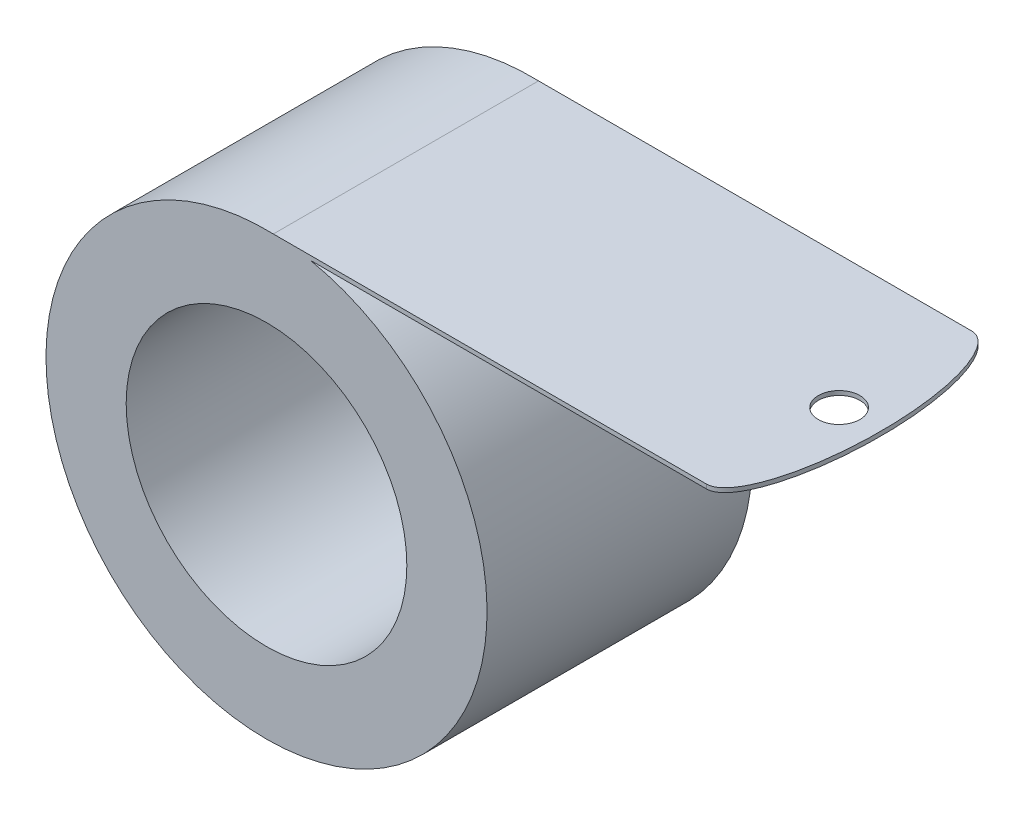
SolidWorks part; units mm, degrees
ref_plane "Front Plane" through (0, 0, 0) normal (0, 0, 1) x (1, 0, 0)
ref_plane "Top Plane" through (0, 0, 0) normal (0, 1, 0) x (1, 0, 0)
ref_plane "Right Plane" through (0, 0, 0) normal (1, 0, 0) x (0, 0, -1)
sketch "Sketch1" plane through (0, 0, 0) normal (0, 0, 1) x (1, 0, 0)
  circle A0 centre (0, 0) radius 26.4033
  circle A1 centre (0, 0) radius 16.8021
  dimension "D1" = 52.8066
  dimension "D2" = 33.6042
extrude "Boss-Extrude1" add sketch "Sketch1" along normal blind 31.75
ref_plane "Plane1" through (0, 25.8826, 0) normal (0, 1, 0) x (1, 0, 0)
sketch "Sketch2" plane through (0, 25.8826, 0) normal (0, 1, 0) x (1, 0, 0)
  line L0 (-26.4033, -31.75) -> (26.4033, -31.75) construction
  line L1 (-26.4033, -31.75) -> (26.4033, -31.75) construction
  line L2 (26.4033, 0) -> (-26.4033, 0) construction
  line L3 (26.4033, 0) -> (-26.4033, 0) construction
  line L4 (0, -31.75) -> (0, 0)
  line L5 (0, 0) -> (52.6814, 0)
  line L6 (0, -31.75) -> (52.6814, -31.75)
  circle A0 centre (52.6814, -15.875) radius 2.4892
  ellipse E0 centre (52.6814, -15.875) end of major axis (52.6814, 0) minor radius 4.9608 (52.6814, -31.75) -> (52.6814, 0) ccw
  dimension "D1" = 4.9784
extrude "Boss-Extrude2" add sketch "Sketch2" along normal blind 0.508
